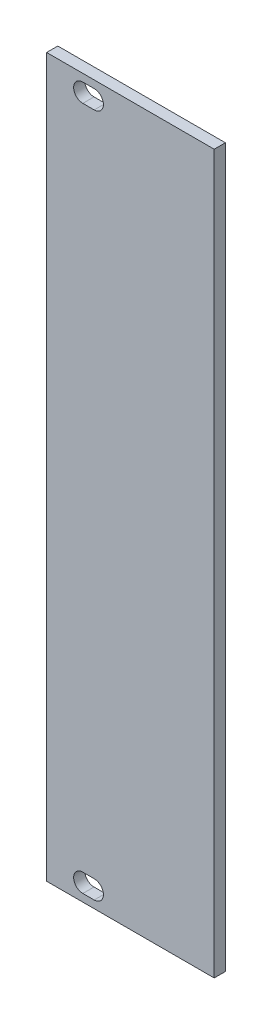
SolidWorks part; units mm, degrees
ref_plane "Front Plane" through (0, 0, 0) normal (0, 0, 1) x (1, 0, 0)
ref_plane "Top Plane" through (0, 0, 0) normal (0, 1, 0) x (1, 0, 0)
ref_plane "Right Plane" through (0, 0, 0) normal (1, 0, 0) x (0, 0, -1)
sketch "Sketch1" plane through (0, 0, 0) normal (0, 0, 1) x (1, 0, 0)
  line L0 (-7.5, 64.25) -> (-7.5, -64.25) construction
  line L1 (-15, 64.25) -> (15, 64.25)
  line L2 (-15, 64.25) -> (-15, -64.25)
  line L3 (-15, -64.25) -> (15, -64.25)
  line L4 (15, 64.25) -> (15, -64.25)
  line L5 (-15, 64.25) -> (15, -64.25) construction
  line L6 (-15, -64.25) -> (15, 64.25) construction
  line L7 (-15, 61.25) -> (15, 61.25) construction
  line L8 (-15, -61.25) -> (15, -61.25) construction
  line L9 (-8.516, -61.25) -> (-6.484, -61.25) construction
  line L11 (-8.516, -59.6) -> (-6.484, -59.6)
  line L12 (-8.516, -62.9) -> (-6.484, -62.9)
  line L13 (-8.516, 61.25) -> (-6.484, 61.25) construction
  line L14 (-8.516, 62.9) -> (-6.484, 62.9)
  line L15 (-8.516, 59.6) -> (-6.484, 59.6)
  arc A0 (-8.516, -59.6) -> (-8.516, -62.9) centre (-8.516, -61.25) ccw
  arc A1 (-6.484, -62.9) -> (-6.484, -59.6) centre (-6.484, -61.25) ccw
  arc A2 (-8.516, 62.9) -> (-8.516, 59.6) centre (-8.516, 61.25) ccw
  arc A3 (-6.484, 59.6) -> (-6.484, 62.9) centre (-6.484, 61.25) ccw
  point P0 (0, 0)
  point P18 (-7.5, -61.25)
  point P24 (-7.5, 61.25)
  dimension "D6" = 1.65
  dimension "D7" = 1.65
  dimension "D1" = 128.5
  dimension "D2" = 30
  dimension "D3" = 7.5
  dimension "D4" = 3
  dimension "D8" = 2.032
  dimension "D9" = 2.032
  dimension "D5" = 3
extrude "Boss-Extrude1" add sketch "Sketch1" along normal blind 2
